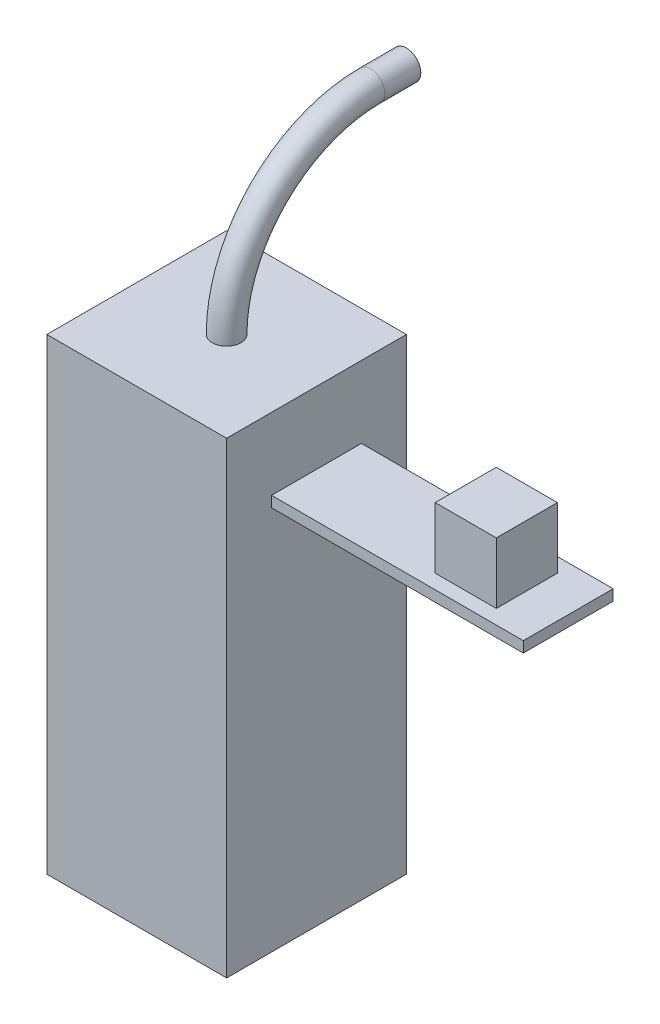
SolidWorks part; units mm, degrees
ref_plane "Plano frontal" through (0, 0, 0) normal (0, 0, 1) x (1, 0, 0)
ref_plane "Plano superior" through (0, 0, 0) normal (0, 1, 0) x (1, 0, 0)
ref_plane "Plano direito" through (0, 0, 0) normal (1, 0, 0) x (0, 0, -1)
sketch "Esboço1" plane through (0, 0, 0) normal (0, 1, 0) x (1, 0, 0)
  line L1 (25, 25) -> (-25, 25)
  line L2 (25, 25) -> (25, -25)
  line L3 (25, -25) -> (-25, -25)
  line L4 (-25, 25) -> (-25, -25)
  line L5 (25, 25) -> (-25, -25) construction
  line L6 (25, -25) -> (-25, 25) construction
  point P0 (0, 0)
  dimension "D1" = 50
  dimension "D2" = 50
extrude "Ressalto-extrusão1" add sketch "Esboço1" along normal blind 130
sketch "Esboço2" plane through (25, 0, 0) normal (1, 0, 0) x (0, 0, -1)
  line L0 (-25, 130) -> (25, 130) construction
  line L1 (-12.5, 110) -> (12.5, 110)
  line L2 (-12.5, 110) -> (-12.5, 107)
  line L3 (-12.5, 107) -> (12.5, 107)
  line L4 (12.5, 110) -> (12.5, 107)
  line L5 (-12.5, 110) -> (12.5, 107) construction
  line L6 (-12.5, 107) -> (12.5, 110) construction
  point P0 (0, 108.5)
  point P7 (0, 130)
  point P8 (0, 0)
  point P9 (0, 0)
  dimension "D1" = 3
  dimension "D2" = 25
  dimension "D3" = 20
extrude "Ressalto-extrusão2" add sketch "Esboço2" along normal blind 70
sketch "Esboço4" plane through (0, 110, 0) normal (0, 1, 0) x (1, 0, 0)
  line L0 (25, 12.5) -> (25, -12.5) construction
  line L1 (83.5, 8.5) -> (66.5, 8.5)
  line L2 (83.5, 8.5) -> (83.5, -8.5)
  line L3 (83.5, -8.5) -> (66.5, -8.5)
  line L4 (66.5, 8.5) -> (66.5, -8.5)
  line L5 (83.5, 8.5) -> (66.5, -8.5) construction
  line L6 (83.5, -8.5) -> (66.5, 8.5) construction
  point P0 (75, 0)
  point P5 (25, 0)
  point P6 (0, 0)
  dimension "D1" = 50
  dimension "D2" = 17
  dimension "D3" = 17
extrude "Ressalto-extrusão3" add sketch "Esboço4" along normal blind 17
sketch "Esboço5" plane through (0, 130, 0) normal (0, 1, 0) x (1, 0, 0)
  circle A0 centre (0, 0) radius 4
  dimension "D1" = 8
sketch "Esboço6" plane through (0, 0, 0) normal (1, 0, 0) x (0, 0, -1)
  line L0 (4, 130) -> (-4, 130) construction
  line L1 (40, 170) -> (50, 170)
  arc A0 (0, 130) -> (40, 170) centre (40, 130) cw
  dimension "D1" = 40
  dimension "D2" = 10
sweep "Varredura1" add profiles "Esboço5" path "Esboço6"
